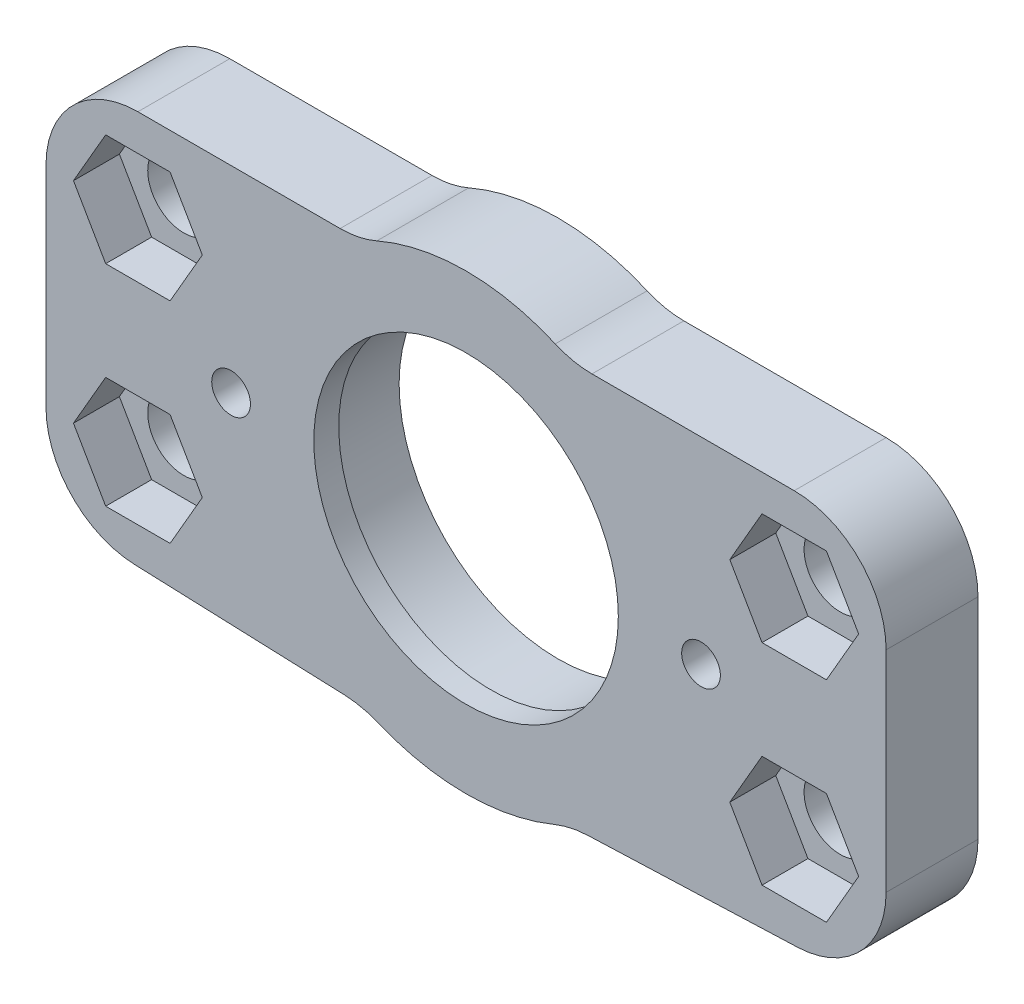
SolidWorks part; units mm, degrees
ref_plane "Спереди" through (0, 0, 0) normal (0, 0, 1) x (1, 0, 0)
ref_plane "Сверху" through (0, 0, 0) normal (0, 1, 0) x (1, 0, 0)
ref_plane "Справа" through (0, 0, 0) normal (1, 0, 0) x (0, 0, -1)
sketch "Эскиз1" plane through (0, 0, 0) normal (0, 0, 1) x (1, 0, 0)
  line L0 (-32, 0) -> (32, 0) construction
  line L1 (-9.2823, -15.6024) -> (-25.2658, -14.995)
  line L2 (-32, 15) -> (-8, 15)
  line L3 (0, 17) -> (0, -17.5) construction
  line L4 (8, 15) -> (32, 15)
  line L5 (-32, -8) -> (-32, 15)
  line L6 (32, 15) -> (32, -8)
  line L7 (-9.5671, -23.097) -> (0, 0) construction
  line L8 (9.2823, -15.6024) -> (25.2658, -14.995)
  line L10 (0, 0) -> (9.5671, -23.097) construction
  circle A0 centre (0, 0) radius 12 construction
  circle A1 centre (0, 0) radius 12.1
  arc A2 (-32, -8) -> (-25.2658, -14.995) centre (-25, -8) ccw
  arc A3 (-9.5671, -23.097) -> (9.5671, -23.097) centre (0, 0) ccw construction
  circle A4 centre (-9.5671, -23.097) radius 7 construction
  arc A5 (-8, 15) -> (8, 15) centre (0, 0) cw
  arc A6 (6.697, -16.1679) -> (-6.697, -16.1679) centre (0, 0) cw
  circle A7 centre (9.5671, -23.097) radius 7 construction
  arc A8 (-6.697, -16.1679) -> (-9.2823, -15.6024) centre (-9.5671, -23.097) ccw
  arc A9 (6.697, -16.1679) -> (9.2823, -15.6024) centre (9.5671, -23.097) cw
  arc A10 (32, -8) -> (25.2658, -14.995) centre (25, -8) cw
  arc A15 (8, 15) -> (-8, 15) centre (0, 0) ccw construction
  dimension "D1" = 24
  dimension "D4" = 5
  dimension "D7" = 30
  dimension "D2" = 0.5
  dimension "D8" = 45
  dimension "D6" = 25
  dimension "D5" = 7
  dimension "D10" = 14
  dimension "D9" = 25
  dimension "D3" = 8
extrude "Бобышка-Вытянуть1" add sketch "Эскиз1" along normal blind 7
ref_plane "Плоскость1" through (0, 0, 5) normal (0, 0, -1) x (-1, 0, 0)
fillet "Скругление3" radius 7 4 edges at (8, 15, 3.5) (-8, 15, 3.5) (-32, 15, 3.5) (32, 15, 3.5)
hole_wizard "Цековка для винта с внутренним шестигранником M51" [suppressed] positions "Эскиз6" profile "Эскиз5" counterbore size "M5" standard "Ansi Metric"
sketch "Эскиз6" plane through (0, 0, 7) normal (0, 0, 1) x (1, 0, 0)
  line L0 (0, 0) -> (-32, 0) construction
  line L1 (-32, 8) -> (-32, -20) construction
  arc A0 (32, 8) -> (25, 15) centre (25, 8) ccw construction
  arc A1 (-25, 15) -> (-32, 8) centre (-25, 8) ccw construction
  point P2 (-25, 8)
  point P29 (25, 8)
  point P59 (25, -8)
  point P60 (-25, -8)
sketch "Эскиз5" plane through (-25, 8, 7) normal (1, 0, 0) x (0, -1, 0)
  line L0 (0, 0) -> (0, 7)
  line L1 (0, 7) -> (2.75, 7)
  line L3 (2.75, 7) -> (2.75, 3.5)
  line L4 (2.75, 3.5) -> (5.1, 3.5)
  line L5 (5.1, 3.5) -> (5.1, 0)
  line L7 (5.1, 0) -> (0, 0)
  line L11 (0, -6.35) -> (0, 107.95) construction
  dimension "Диаметр сквозного отверстия" = 5.5
  dimension "Глубина сквозного отверстия" = 7
  dimension "Диаметр цековки" = 10.2
  dimension "Глубина цековки" = 3.5
hole_wizard "Отверстие с зазором M52" [suppressed] positions "Эскиз12" profile "Эскиз11" hole size "M5" standard "Ansi Metric"
sketch "Эскиз12" plane through (0, 0, 7) normal (0, 0, 1) x (1, 0, 0)
  arc A0 (-32, -20) -> (-19.2137, -23.9393) centre (-25, -20) ccw construction
  arc A1 (19.2137, -23.9393) -> (32, -20) centre (25, -20) ccw construction
  point P0 (-25, -20)
  point P2 (25, -20)
sketch "Эскиз11" plane through (-25, -20, 7) normal (1, 0, 0) x (0, -1, 0)
  line L0 (0, 0) -> (0, 27.6524)
  line L1 (0, 27.6524) -> (2.75, 26)
  line L2 (2.75, 26) -> (2.75, 0)
  line L5 (2.75, 0) -> (0, 0)
  line L10 (0, 27.6524) -> (-2.75, 26) construction
  line L11 (0, -6.35) -> (0, 107.95) construction
  dimension "Диаметр отверстия" = 5.5
  dimension "Глубина отверстия" = 26
  dimension "Угол заточки сверла" = 118
sketch "Эскиз7" plane through (0, 0, 7) normal (0, 0, 1) x (1, 0, 0)
  circle A0 centre (0, 0) radius 12.1 construction
  circle A1 centre (0, 0) radius 12.1
  circle A2 centre (0, 0) radius 11.6
  dimension "D1" = 0.5
extrude "Бобышка-Вытянуть2" add sketch "Эскиз7" against normal offset from surface (1.9 mm away) 0.1 up to plane "Плоскость1"
hole_wizard "Отверстие с зазором M53" positions "Эскиз15" profile "Эскиз14" hole size "M5" standard "Ansi Metric" end condition through all
sketch "Эскиз15" plane through (0, 0, 7) normal (0, 0, 1) x (1, 0, 0)
  arc A0 (-25, 15) -> (-32, 8) centre (-25, 8) ccw construction
  arc A1 (32, 8) -> (25, 15) centre (25, 8) ccw construction
  point P0 (-25, 8)
  point P3 (25, 8)
sketch "Эскиз14" plane through (-25, 8, 7) normal (1, 0, 0) x (0, -1, 0)
  line L0 (0, 0) -> (0, 7)
  line L1 (0, 7) -> (2.75, 7)
  line L2 (2.75, 7) -> (2.75, 0)
  line L5 (2.75, 0) -> (0, 0)
  line L11 (0, -6.35) -> (0, 107.95) construction
  dimension "Диаметр сквозного отверстия" = 5.5
  dimension "Глубина сквозного отверстия" = 7
hole_wizard "Отверстие с зазором M54" positions "Эскиз17" profile "Эскиз16" hole size "M5" standard "Ansi Metric" end condition through all
sketch "Эскиз17" plane through (-20.8504, 7.1997, 7) normal (0, 0, -1) x (-1, 0, 0)
  arc A0 (-52.8504, -15.1997) -> (-46.1162, -22.1947) centre (-45.8504, -15.1997) ccw construction
  arc A1 (4.4155, -22.1947) -> (11.1496, -15.1997) centre (4.1496, -15.1997) ccw construction
  point P0 (-45.8504, -15.1997)
  point P2 (4.1496, -15.1997)
sketch "Эскиз16" plane through (25, -8, 7) normal (1, 0, 0) x (0, -1, 0)
  line L0 (0, 0) -> (0, 7)
  line L1 (0, 7) -> (2.75, 7)
  line L2 (2.75, 7) -> (2.75, 0)
  line L5 (2.75, 0) -> (0, 0)
  line L11 (0, -6.35) -> (0, 107.95) construction
  dimension "Диаметр сквозного отверстия" = 5.5
  dimension "Глубина сквозного отверстия" = 7
sketch "Эскиз18" plane through (0, 0, 7) normal (0, 0, -1) x (1, 0, 0)
  line L0 (25, -15) -> (9.5917, -15) construction
  line L1 (20.0925, -8) -> (22.5463, -12.25)
  line L2 (22.5463, -12.25) -> (27.4537, -12.25)
  line L3 (27.4537, -12.25) -> (29.9075, -8)
  line L4 (29.9075, -8) -> (27.4537, -3.75)
  line L5 (27.4537, -3.75) -> (22.5463, -3.75)
  line L6 (22.5463, -3.75) -> (20.0925, -8)
  line L7 (-27.4537, -3.75) -> (-29.9075, -8)
  line L8 (-29.9075, -8) -> (-27.4537, -12.25)
  line L9 (-27.4537, -12.25) -> (-22.5463, -12.25)
  line L10 (-22.5463, -12.25) -> (-20.0925, -8)
  line L11 (-20.0925, -8) -> (-22.5463, -3.75)
  line L12 (-22.5463, -3.75) -> (-27.4537, -3.75)
  line L13 (-32, 0) -> (32, 0) construction
  line L14 (-32, -8) -> (-32, 8) construction
  line L15 (32, 8) -> (32, -8) construction
  line L16 (20.0925, 8) -> (22.5463, 12.25)
  line L17 (22.5463, 12.25) -> (27.4537, 12.25)
  line L18 (27.4537, 12.25) -> (29.9075, 8)
  line L19 (29.9075, 8) -> (27.4537, 3.75)
  line L20 (27.4537, 3.75) -> (22.5463, 3.75)
  line L21 (22.5463, 3.75) -> (20.0925, 8)
  line L22 (-22.5463, 12.25) -> (-20.0925, 8)
  line L23 (-27.4537, 12.25) -> (-22.5463, 12.25)
  line L24 (-29.9075, 8) -> (-27.4537, 12.25)
  line L25 (-27.4537, 3.75) -> (-29.9075, 8)
  line L26 (-20.0925, 8) -> (-22.5463, 3.75)
  line L27 (-22.5463, 3.75) -> (-27.4537, 3.75)
  circle A0 centre (25, -8) radius 4.25 construction
  circle A1 centre (-25, -8) radius 4.25 construction
  dimension "D1" = 8.5
  dimension "D2" = 8.5
extrude "Вырез-Вытянуть1" cut sketch "Эскиз18" along normal blind 3.5
hole_wizard "Сверление под метчик M2x0.41" [suppressed] positions "Эскиз20" profile "Эскиз19" hole size "M2x0.4" standard "Ansi Metric"
sketch "Эскиз20" plane through (0, 8, 0) normal (0, 1, 0) x (1, 0, 0)
  line L0 (0, 0) -> (0, 17) construction
  arc A0 (6.7941, 15.5833) -> (-6.7941, 15.5833) centre (0, 0) ccw construction
  point P0 (-14.5, 0)
  point P2 (14.5, 0)
  dimension "D1" = 14.5
sketch "Эскиз19" plane through (-14.5, 8, 0) normal (1, 0, 0) x (0, 0, 1)
  line L0 (0, 0) -> (0, 8)
  line L1 (0, 8) -> (0.8, 8)
  line L2 (0.8, 8) -> (0.8, 0)
  line L5 (0.8, 0) -> (0, 0)
  line L11 (0, -6.35) -> (0, 107.95) construction
  dimension "Диаметр сквозного отверстия" = 1.6
  dimension "Глубина сквозного отверстия" = 8
sketch "Эскиз21" plane through (0, 0, 7) normal (0, 0, 1) x (1, 0, 0)
  circle A0 centre (0, 0) radius 13.25
  dimension "D1" = 26.5
extrude "Вырез-Вытянуть2" [suppressed] cut sketch "Эскиз21" against normal blind 0.5
sketch "Эскиз22" [suppressed] plane through (0, 0, 7) normal (0, 0, 1) x (1, 0, 0)
  circle A0 centre (25, -20) radius 2.75 construction
  circle A1 centre (25, -20) radius 2.75
  circle A2 centre (-25, -20) radius 2.75 construction
  circle A3 centre (-25, -20) radius 2.75
  circle A4 centre (-25, -20) radius 4.25
  circle A5 centre (25, -20) radius 4.25
  dimension "D1" = 1.5
  dimension "D2" = 1.5
extrude "Бобышка-Вытянуть3" [suppressed] add sketch "Эскиз22" along normal blind 0.5
sketch "Sketch1" plane through (0, 0, 0) normal (0, 0, 1) x (1, 0, 0)
  line L0 (0, 0) -> (17.9, 0) construction
  line L1 (0, 0) -> (0, 11.6) construction
  circle A0 centre (17.9, 0) radius 1.4756
  circle A1 centre (0, 0) radius 11.6 construction
  circle A2 centre (-17.9, 0) radius 1.4756
  dimension "D1" = 17.9
extrude "Cut-Extrude1" cut sketch "Sketch1" along normal blind 10
